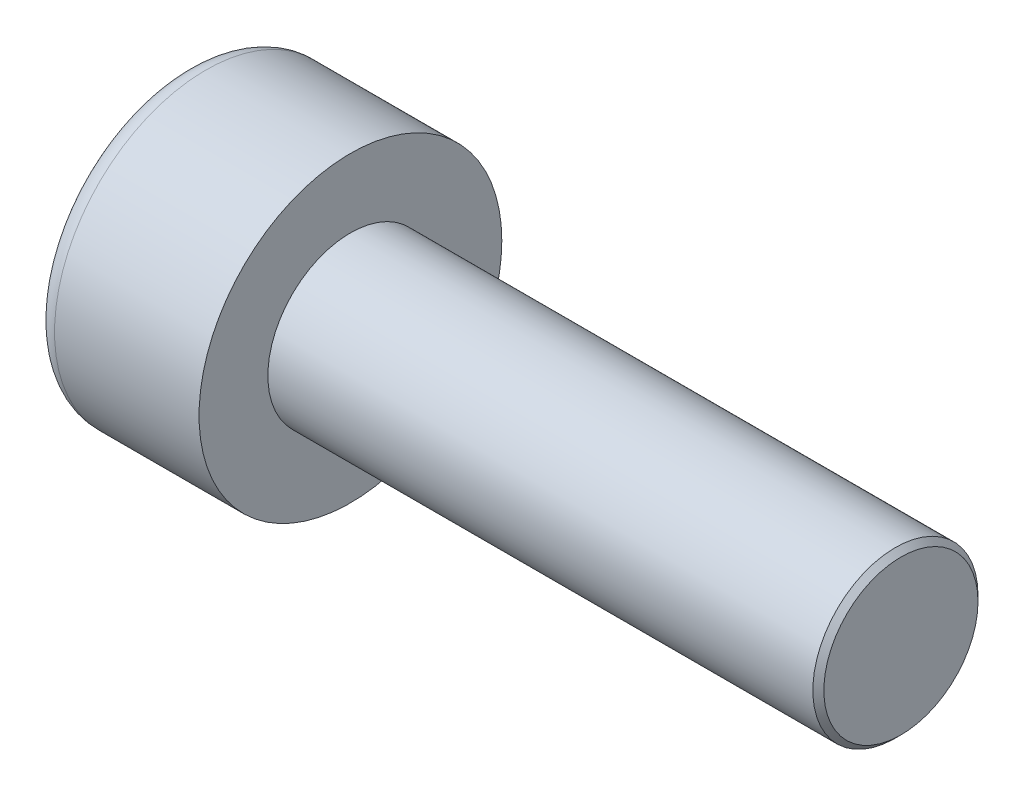
SolidWorks part; units mm, degrees
ref_plane "Front" through (0, 0, 0) normal (0, 0, 1) x (1, 0, 0)
ref_plane "Top" through (0, 0, 0) normal (0, 1, 0) x (1, 0, 0)
ref_plane "Right" through (0, 0, 0) normal (1, 0, 0) x (0, 0, -1)
sketch "Sketch1" plane through (0, 0, 0) normal (1, 0, 0) x (0, 0, -1)
  circle A0 centre (0, 0) radius 2.75
  dimension "dk" = 5.5
extrude "BaseHead" add sketch "Sketch1" along normal blind 3
sketch "Sketch2" plane through (3, 0, 0) normal (1, 0, 0) x (0, 0, -1)
  circle A0 centre (0, 0) radius 1.5
  dimension "d" = 3
extrude "BaseBody" add sketch "Sketch2" along normal blind 10
cosmetic thread "ThreadCosmetic1" parameters "b"=10, "D2"=2.459
sketch "Sketch3" plane through (0, 0, 0) normal (1, 0, 0) x (0, 0, -1)
  line L1 (1.4434, 0) -> (0.7217, 1.25)
  line L2 (0.7217, 1.25) -> (-0.7217, 1.25)
  line L3 (-0.7217, 1.25) -> (-1.4434, 0)
  line L4 (-1.4434, 0) -> (-0.7217, -1.25)
  line L5 (-0.7217, -1.25) -> (0.7217, -1.25)
  line L6 (0.7217, -1.25) -> (1.4434, 0)
  circle A0 centre (0, 0) radius 1.25 construction
  dimension "s" = 2.5
  dimension "e" = 2.8868
extrude "HexagonSocket" cut sketch "Sketch3" along normal blind 1.3
sketch "Sketch4" plane through (-4.1961, 0.75, 0) normal (0, 0, 1) x (-1, 0, 0)
  line L0 (-5.4961, 2) -> (-6.2178, 0.75)
  line L2 (-6.2178, 0.75) -> (-5.4961, 0.75)
  line L3 (-5.4961, 0.75) -> (-5.4961, 2)
  line L4 (-5.0351, 0.75) -> (0.839, 0.75) construction
  line L5 (-17.1961, 0.75) -> (-7.1961, 0.75) construction
  line L6 (-7.1961, 0.75) -> (-4.1961, 0.75) construction
  dimension "m" = 60
revolve "Cut-Revolve1" cut sketch "Sketch4" angle 360 about L4
fillet "HeadFillet" [suppressed] radius 0.1
fillet "TopFillet" radius 0.375 1 edges at (0, 0, -2.75)
chamfer "Chamfer1" distance 0.1 angle 45 1 edges at (13, 0, -1.5)
sketch "Sketch5" plane through (0, 0, 0) normal (0, 0, 1) x (1, 0, 0)
  line L0 (12.9, 1.2657) -> (13.0352, 1.5)
  line L1 (13.0352, 1.5) -> (13.0352, 1.7705)
  line L2 (13.0352, 1.7705) -> (12.7647, 1.7705)
  line L3 (12.7647, 1.7705) -> (12.7647, 1.5)
  line L4 (12.7647, 1.5) -> (12.9, 1.2657)
  line L5 (0, 0) -> (7.8886, 0) construction
  line L6 (12.9, -1.5) -> (12.9, 1.5) construction
  dimension "D1" = 3
  dimension "D2" = 0.2705
revolve "Cut-Revolve10" [suppressed] cut sketch "Sketch5" angle 360 about L5
pattern_linear "LPattern10" [suppressed] count 31 spacing 0.3246 along (1, 0, 0)
equation "\"r1@TopFillet\" = \"d@Sketch2\" / 8"
equation "\"D1@Chamfer1\" = \"r@HeadFillet\""
equation "\"D1@Sketch5\" = \"d@Sketch2\""
equation "\"D2@Sketch5\" =  ( \"d@Sketch2\" - \"D2@ThreadCosmetic1\" )  / 2"
equation "\"D3@LPattern10\" = \"D2@Sketch5\" * 1.2"
equation "\"D1@LPattern10\" = \"b@ThreadCosmetic1\" / \"D3@LPattern10\""
